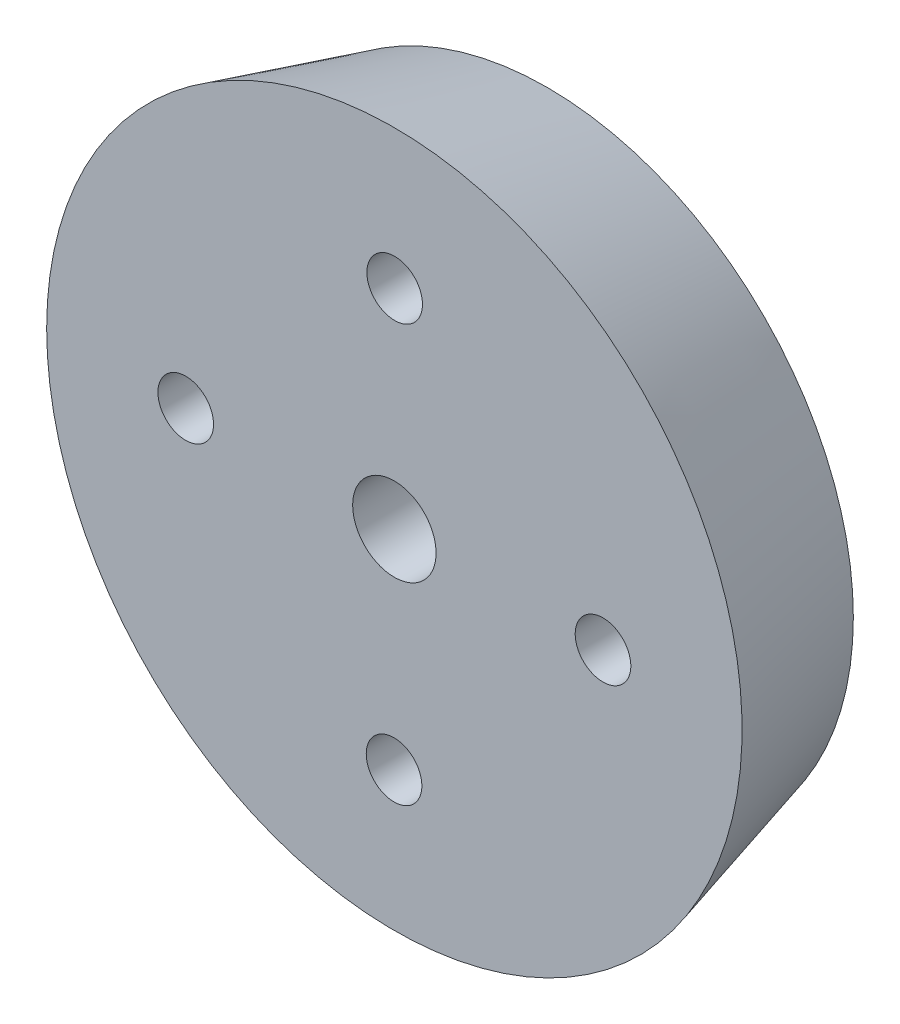
SolidWorks part; units mm, degrees
ref_plane "Front Plane" through (0, 0, 0) normal (0, 0, 1) x (1, 0, 0)
ref_plane "Top Plane" through (0, 0, 0) normal (0, 1, 0) x (1, 0, 0)
ref_plane "Right Plane" through (0, 0, 0) normal (1, 0, 0) x (0, 0, -1)
ref_plane "Plane1" through (0, 0, 0) normal (0, -1, 0) x (1, 0, 0)
sketch "Sketch1" plane through (0, 0, 0) normal (0, -1, 0) x (1, 0, 0)
  line L0 (25, -94) -> (0, -94)
  line L1 (0, -94) -> (0, -105)
  line L2 (0, -105) -> (22, -105)
  line L3 (22, -105) -> (25, -94)
  line L4 (0, -94) -> (0, -105) construction
revolve "Revolve1" add sketch "Sketch1" angle 360 about L4
hole_wizard "Ø4.0 (4) Diameter Hole1" positions "Sketch3" profile "Sketch2" hole size "Ø4.0" standard "ANSI Metric"
sketch "Sketch3" plane through (0, 0, -105) normal (0, 0, -1) x (-1, 0, 0)
  point P0 (-15, -0.0229)
  point P1 (0.0229, -15)
  point P2 (-0.0229, 15)
  point P3 (15, 0.0229)
sketch "Sketch2" plane through (15, -0.0229, -105) normal (1, 0, 0) x (0, 1, 0)
  line L0 (0, 0) -> (0, 11)
  line L1 (0, 11) -> (2, 11)
  line L2 (2, 11) -> (2, 0)
  line L5 (2, 0) -> (0, 0)
  line L11 (0, -6.35) -> (0, 107.95) construction
  dimension "Thru Hole Dia." = 4
  dimension "Thru Hole Depth" = 11
sketch "Sketch4" plane through (0, 0, -105) normal (0, 0, -1) x (-1, 0, 0)
  circle A0 centre (0, 0) radius 3
  dimension "D1" = 6
extrude "Cut-Extrude1" cut sketch "Sketch4" against normal through all
